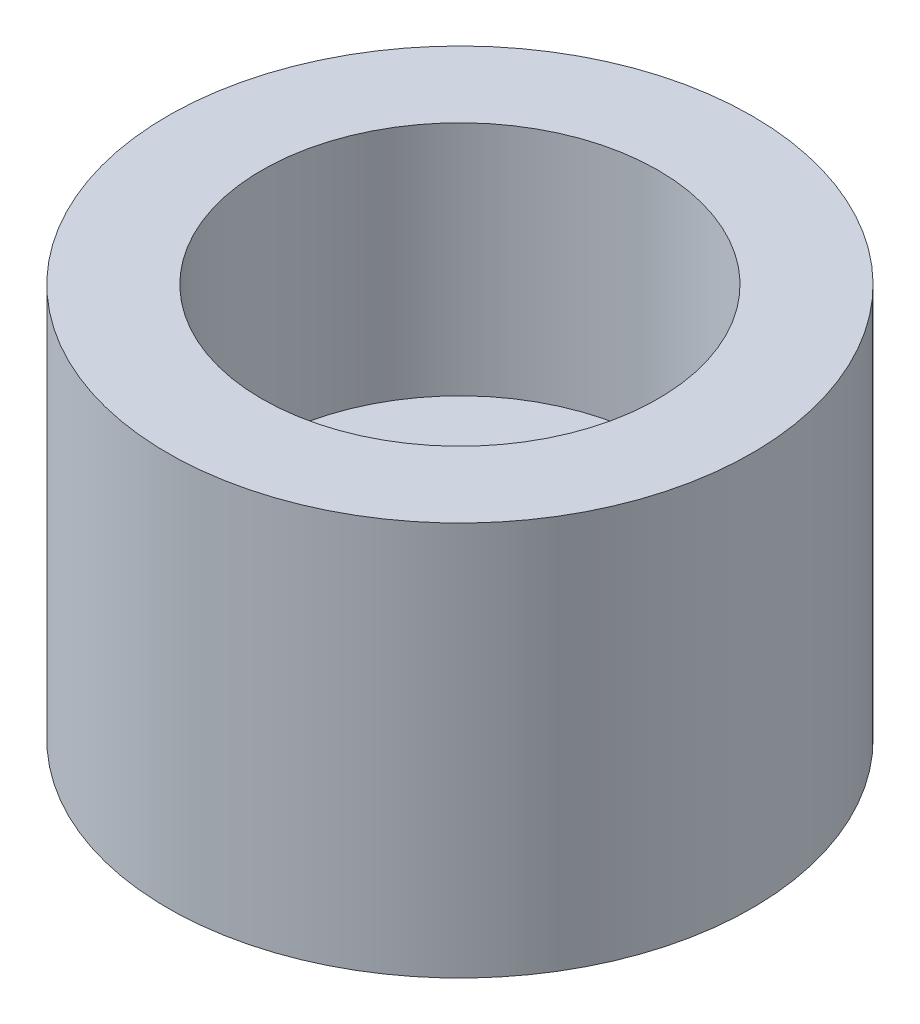
SolidWorks part; units mm, degrees
ref_plane "Front Plane" through (0, 0, 0) normal (0, 0, 1) x (1, 0, 0)
ref_plane "Top Plane" through (0, 0, 0) normal (0, 1, 0) x (1, 0, 0)
ref_plane "Right Plane" through (0, 0, 0) normal (1, 0, 0) x (0, 0, -1)
sketch "Sketch2" plane through (0, 0, 0) normal (0, 0, 1) x (1, 0, 0)
  line L0 (0, 0) -> (0, 9.525) construction
  line L1 (2.3813, -4.7625) -> (7.0612, -4.7625)
  line L2 (2.3813, -4.7625) -> (2.3812, 4.7625)
  line L3 (2.3812, 4.7625) -> (7.0612, 4.7625)
  line L4 (7.0612, -4.7625) -> (7.0612, 4.7625)
  line L6 (2.3812, 4.7625) -> (4.7879, 4.7625)
  line L7 (2.3812, 4.7625) -> (2.3813, -0.9525)
  line L8 (2.3813, -0.9525) -> (4.7879, -0.9525)
  line L9 (4.7879, 4.7625) -> (4.7879, -0.9525)
  point P8 (2.3813, 0)
  dimension "D1" = 7.0612
  dimension "D2" = 2.3813
  dimension "D3" = 9.525
  dimension "D4" = 4.7879
  dimension "D5" = 5.715
revolve "Revolve1" add sketch "Sketch2" angle 360 about L0
